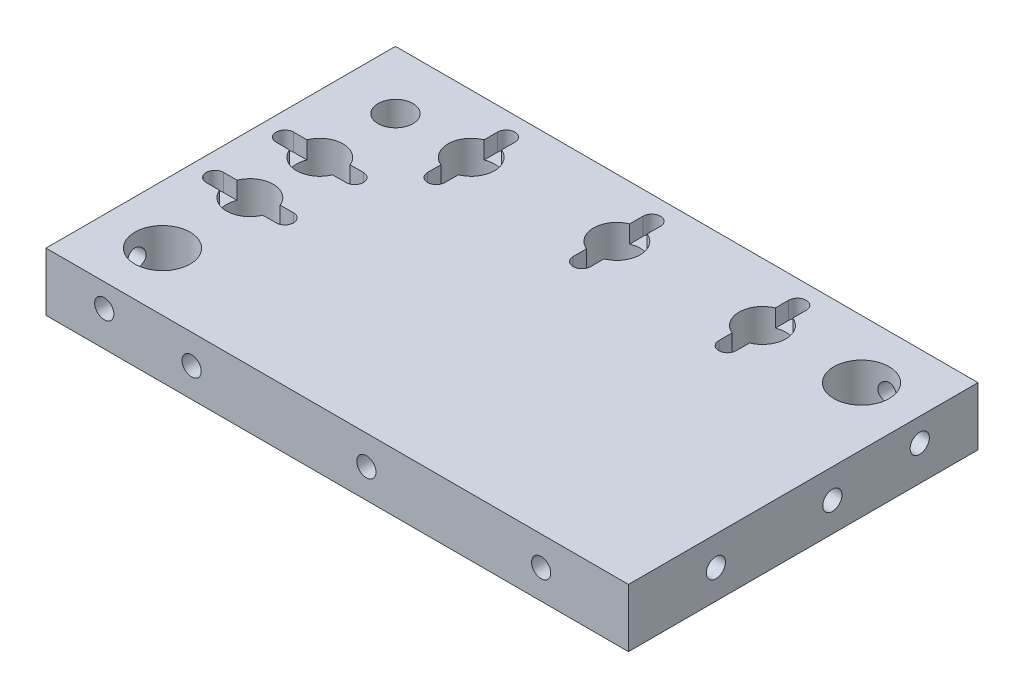
SolidWorks part; units mm, degrees
material "7075-T6, Plate (SS)"
ref_plane "Front Plane" through (0, 0, 0) normal (0, 0, 1) x (1, 0, 0)
ref_plane "Top Plane" through (0, 0, 0) normal (0, 1, 0) x (1, 0, 0)
ref_plane "Right Plane" through (0, 0, 0) normal (1, 0, 0) x (0, 0, -1)
sketch "Sketch1" plane through (0, 0, 0) normal (0, 1, 0) x (1, 0, 0)
  line L1 (-50, -30) -> (50, -30)
  line L2 (-50, -30) -> (-50, 30)
  line L3 (-50, 30) -> (50, 30)
  line L4 (50, -30) -> (50, 30)
  line L5 (-50, -30) -> (50, 30) construction
  line L6 (-50, 30) -> (50, -30) construction
  point P0 (0, 0)
  dimension "D1" = 100
  dimension "D2" = 60
extrude "Boss-Extrude1" add sketch "Sketch1" along normal blind 10
sketch "Sketch2" plane through (0, 10, 0) normal (0, 1, 0) x (1, 0, 0)
  line L0 (50, 30) -> (-50, 30) construction
  line L1 (-50, 30) -> (-50, -30) construction
  circle A0 centre (-40, 20) radius 3
  circle A1 centre (-27, 20) radius 4
  circle A2 centre (-2, 20) radius 4
  circle A3 centre (23, 20) radius 4
  circle A4 centre (40, 20) radius 4.75
  circle A5 centre (-40, 7) radius 4
  circle A6 centre (-40, -5) radius 4
  circle A7 centre (-40, -20) radius 4.75
  dimension "D3" = 6
  dimension "D4" = 8
  dimension "D5" = 23
  dimension "D6" = 35
  dimension "D7" = 50
  dimension "D8" = 9.5
  dimension "D9" = 23
  dimension "D10" = 48
  dimension "D11" = 73
  dimension "D12" = 90
  dimension "D1" = 10
  dimension "D2" = 10
extrude "Cut-Extrude1" cut sketch "Sketch2" against normal up to next
sketch "Sketch3" plane through (0, 10, 0) normal (0, 1, 0) x (1, 0, 0)
  line L0 (-46, 7) -> (-34, 7) construction
  line L1 (-46, 8.5) -> (-34, 8.5)
  line L2 (-46, 5.5) -> (-34, 5.5)
  line L3 (-46, -5) -> (-34, -5) construction
  line L4 (-46, -3.5) -> (-34, -3.5)
  line L5 (-46, -6.5) -> (-34, -6.5)
  line L6 (-27, 26) -> (-27, 14) construction
  line L7 (-25.5, 26) -> (-25.5, 14)
  line L8 (-28.5, 26) -> (-28.5, 14)
  line L9 (-2, 26) -> (-2, 14) construction
  line L10 (-0.5, 26) -> (-0.5, 14)
  line L11 (-3.5, 26) -> (-3.5, 14)
  line L12 (23, 26) -> (23, 14) construction
  line L13 (24.5, 26) -> (24.5, 14)
  line L14 (21.5, 26) -> (21.5, 14)
  arc A0 (-46, 8.5) -> (-46, 5.5) centre (-46, 7) ccw
  arc A1 (-34, 5.5) -> (-34, 8.5) centre (-34, 7) ccw
  arc A2 (-46, -3.5) -> (-46, -6.5) centre (-46, -5) ccw
  arc A3 (-34, -6.5) -> (-34, -3.5) centre (-34, -5) ccw
  arc A4 (-25.5, 26) -> (-28.5, 26) centre (-27, 26) ccw
  arc A5 (-28.5, 14) -> (-25.5, 14) centre (-27, 14) ccw
  arc A6 (-0.5, 26) -> (-3.5, 26) centre (-2, 26) ccw
  arc A7 (-3.5, 14) -> (-0.5, 14) centre (-2, 14) ccw
  arc A8 (24.5, 26) -> (21.5, 26) centre (23, 26) ccw
  arc A9 (21.5, 14) -> (24.5, 14) centre (23, 14) ccw
  point P2 (-40, 7)
  point P9 (-40, -5)
  point P17 (-27, 20)
  point P25 (-2, 20)
  point P33 (23, 20)
  dimension "D1" = 12
  dimension "D2" = 3
extrude "Cut-Extrude2" cut sketch "Sketch3" against normal blind 3
hole_wizard "M4 Tapped Hole1" positions "Sketch4" profile "Sketch5" tap size "M4" standard "DIN"
sketch "Sketch4" plane through (-50, 0, 0) normal (-1, 0, 0) x (0, 0, 1)
  line L0 (-30, 10) -> (30, 10) construction
  line L1 (30, 10) -> (30, 0) construction
  point P0 (20, 6)
  dimension "D1" = 4
  dimension "D2" = 10
sketch "Sketch5" plane through (-50, 6, 20) normal (0, 1, 0) x (0, 0, 1)
  line L0 (0, 0) -> (0, 12.9914)
  line L1 (0, 12.9914) -> (1.65, 12)
  line L2 (1.65, 12) -> (1.65, 0)
  line L5 (1.65, 0) -> (0, 0)
  line L10 (0, 12.9914) -> (-1.65, 12) construction
  line L11 (0, -6.35) -> (0, 107.95) construction
  dimension "Tap Drill Dia." = 3.3
  dimension "Tap Drill Depth" = 12
  dimension "Drill Angle" = 118
cosmetic thread "Hole Thread1" parameters "D1"=5.5458, "D2"=4
hole_wizard "M4 Tapped Hole2" positions "Sketch6" profile "Sketch7" tap size "M4" standard "DIN"
sketch "Sketch6" plane through (0, 0, 30) normal (0, 0, 1) x (1, 0, 0)
  line L0 (50, 10) -> (50, 0) construction
  line L1 (-50, 10) -> (50, 10) construction
  line L2 (-50, 10) -> (-50, 0) construction
  point P0 (-40, 6)
  point P2 (-25, 5)
  point P4 (5, 5)
  point P6 (35, 5)
  point P12 (50, 5)
  dimension "D1" = 4
  dimension "D2" = 10
  dimension "D3" = 25
  dimension "D4" = 55
  dimension "D5" = 85
sketch "Sketch7" plane through (-40, 6, 30) normal (1, 0, 0) x (0, -1, 0)
  line L0 (0, 0) -> (0, 12.9914)
  line L1 (0, 12.9914) -> (1.65, 12)
  line L2 (1.65, 12) -> (1.65, 0)
  line L5 (1.65, 0) -> (0, 0)
  line L10 (0, 12.9914) -> (-1.65, 12) construction
  line L11 (0, -6.35) -> (0, 107.95) construction
  dimension "Tap Drill Dia." = 3.3
  dimension "Tap Drill Depth" = 12
  dimension "Drill Angle" = 118
cosmetic thread "Hole Thread2" parameters "D1"=9, "D2"=4
cosmetic thread "Hole Thread3" parameters "D1"=9, "D2"=4
cosmetic thread "Hole Thread4" parameters "D1"=9, "D2"=4
cosmetic thread "Hole Thread5" parameters "D1"=5.5458, "D2"=4
hole_wizard "M4 Tapped Hole3" positions "Sketch8" profile "Sketch9" tap size "M4" standard "DIN"
sketch "Sketch8" plane through (50, 0, 0) normal (1, 0, 0) x (0, 0, -1)
  line L0 (-30, 10) -> (30, 10) construction
  line L1 (30, 10) -> (30, 0) construction
  line L2 (-30, 10) -> (-30, 0) construction
  point P0 (-15, 5)
  point P2 (5, 5)
  point P4 (20, 6)
  point P25 (-30, 5)
  dimension "D1" = 4
  dimension "D2" = 10
  dimension "D3" = 25
  dimension "D4" = 45
sketch "Sketch9" plane through (50, 5, 15) normal (0, 1, 0) x (0, 0, -1)
  line L0 (0, 0) -> (0, 12.9914)
  line L1 (0, 12.9914) -> (1.65, 12)
  line L2 (1.65, 12) -> (1.65, 0)
  line L5 (1.65, 0) -> (0, 0)
  line L10 (0, 12.9914) -> (-1.65, 12) construction
  line L11 (0, -6.35) -> (0, 107.95) construction
  dimension "Tap Drill Dia." = 3.3
  dimension "Tap Drill Depth" = 12
  dimension "Drill Angle" = 118
cosmetic thread "Hole Thread6" parameters "D1"=5.5458, "D2"=4
cosmetic thread "Hole Thread7" parameters "D1"=9, "D2"=4
cosmetic thread "Hole Thread8" parameters "D1"=9, "D2"=4
hole_wizard "M4 Tapped Hole4" positions "Sketch10" profile "Sketch11" tap size "M4" standard "DIN"
sketch "Sketch10" plane through (0, 0, -30) normal (0, 0, -1) x (-1, 0, 0)
  line L0 (-50, 10) -> (50, 10) construction
  line L1 (-50, 10) -> (-50, 0) construction
  point P0 (-40, 6)
  dimension "D1" = 4
  dimension "D2" = 10
sketch "Sketch11" plane through (40, 6, -30) normal (1, 0, 0) x (0, 1, 0)
  line L0 (0, 0) -> (0, 12.9914)
  line L1 (0, 12.9914) -> (1.65, 12)
  line L2 (1.65, 12) -> (1.65, 0)
  line L5 (1.65, 0) -> (0, 0)
  line L10 (0, 12.9914) -> (-1.65, 12) construction
  line L11 (0, -6.35) -> (0, 107.95) construction
  dimension "Tap Drill Dia." = 3.3
  dimension "Tap Drill Depth" = 12
  dimension "Drill Angle" = 118
cosmetic thread "Hole Thread9" parameters "D1"=5.5458, "D2"=4
